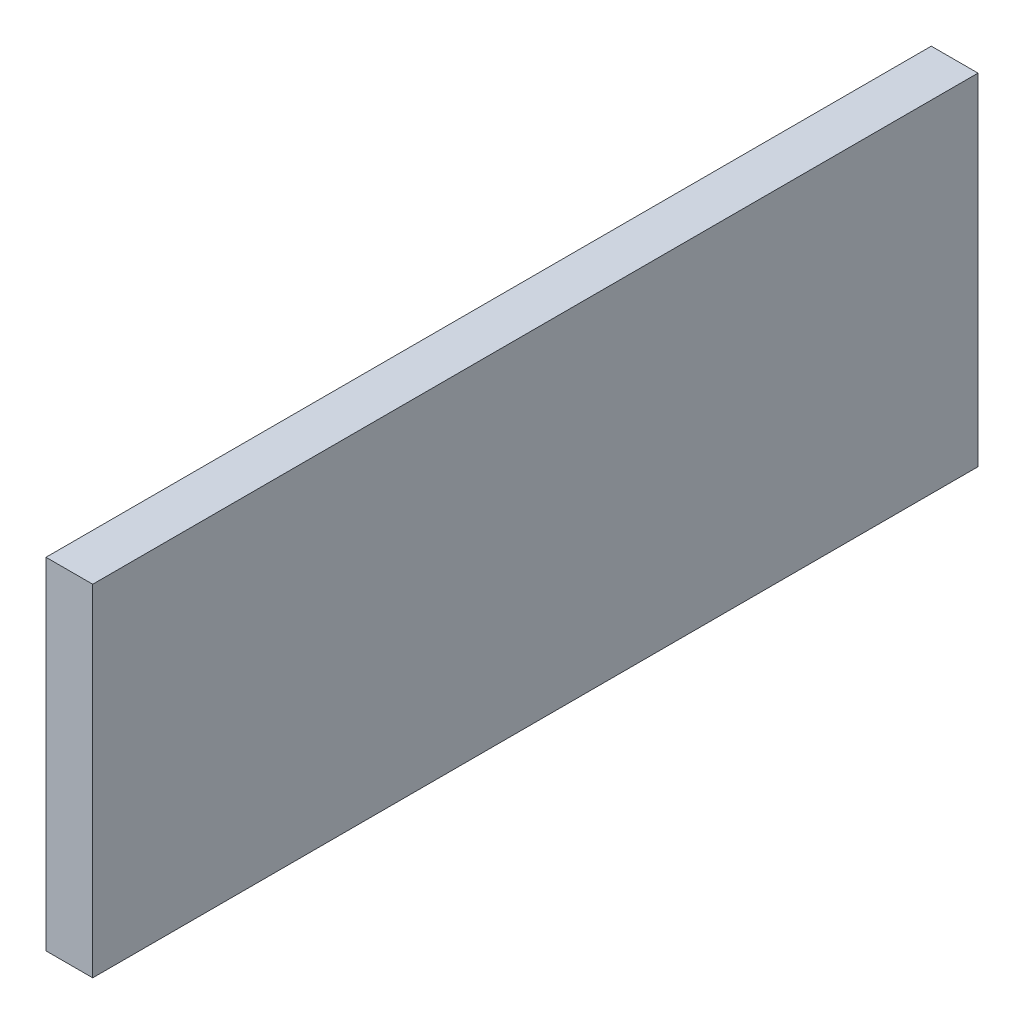
SolidWorks part; units mm, degrees
material "Maple"
ref_plane "Front Plane" through (0, 0, 0) normal (0, 0, 1) x (1, 0, 0)
ref_plane "Top Plane" through (0, 0, 0) normal (0, 1, 0) x (1, 0, 0)
ref_plane "Right Plane" through (0, 0, 0) normal (1, 0, 0) x (0, 0, -1)
sketch "Sketch1" plane through (0, 0, 0) normal (0, 0, 1) x (1, 0, 0)
  line L1 (-1.5875, 11.585) -> (1.5875, 11.585)
  line L2 (-1.5875, 11.585) -> (-1.5875, -11.585)
  line L3 (-1.5875, -11.585) -> (1.5875, -11.585)
  line L4 (1.5875, 11.585) -> (1.5875, -11.585)
  line L5 (-1.5875, 11.585) -> (1.5875, -11.585) construction
  line L6 (-1.5875, -11.585) -> (1.5875, 11.585) construction
  point P0 (0, 0)
  dimension "D1" = 3.175
  dimension "D2" = 23.17
extrude "Boss-Extrude1" add sketch "Sketch1" along normal blind 60.17
equation "\"kerf\"= 0.17 / 2"
